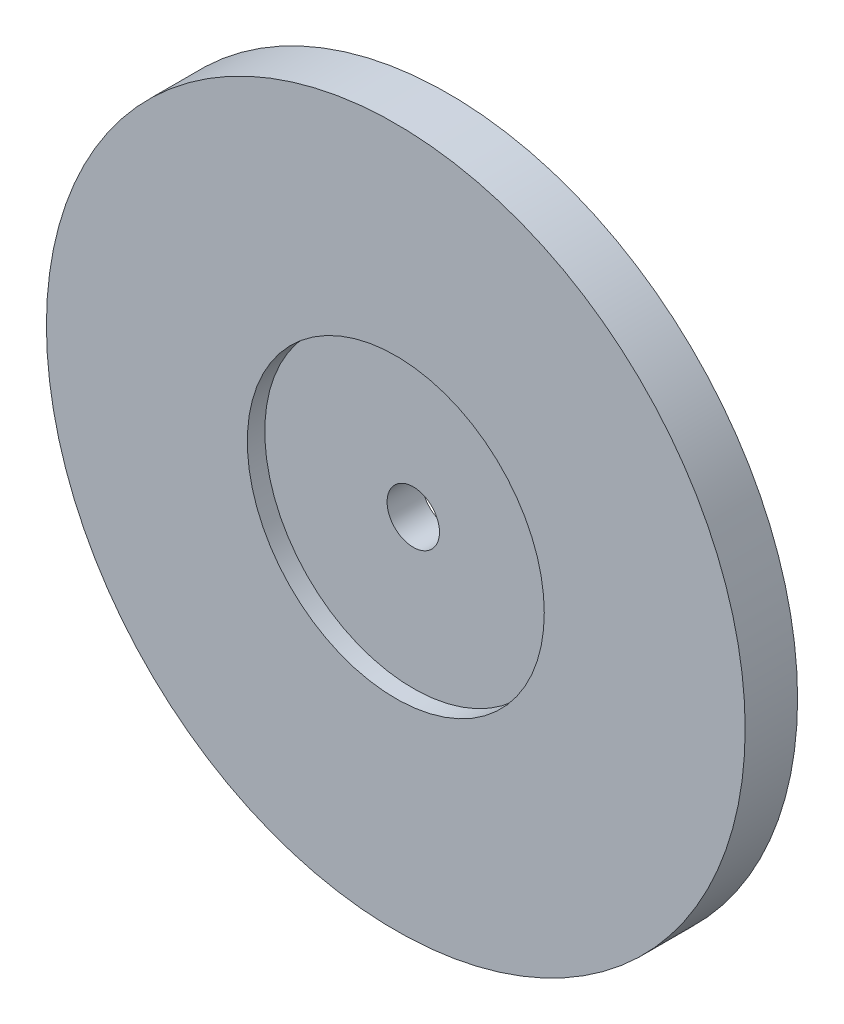
SolidWorks part; units mm, degrees
ref_plane "Alzado" through (0, 0, 0) normal (0, 0, 1) x (1, 0, 0)
ref_plane "Planta" through (0, 0, 0) normal (0, 1, 0) x (1, 0, 0)
ref_plane "Vista lateral" through (0, 0, 0) normal (1, 0, 0) x (0, 0, -1)
sketch "Croquis1" plane through (0, 0, 0) normal (0, 0, 1) x (1, 0, 0)
  circle A0 centre (-67.943, 10.1636) radius 20
  circle A1 centre (-67.943, 10.1636) radius 1.5
extrude "Saliente-Extruir1" add sketch "Croquis1" along normal blind 3
sketch "Croquis2" plane through (0, 0, 3) normal (0, 0, 1) x (1, 0, 0)
  circle A0 centre (-67.943, 10.1636) radius 8.5
extrude "Cortar-Extruir1" cut sketch "Croquis2" against normal blind 1
